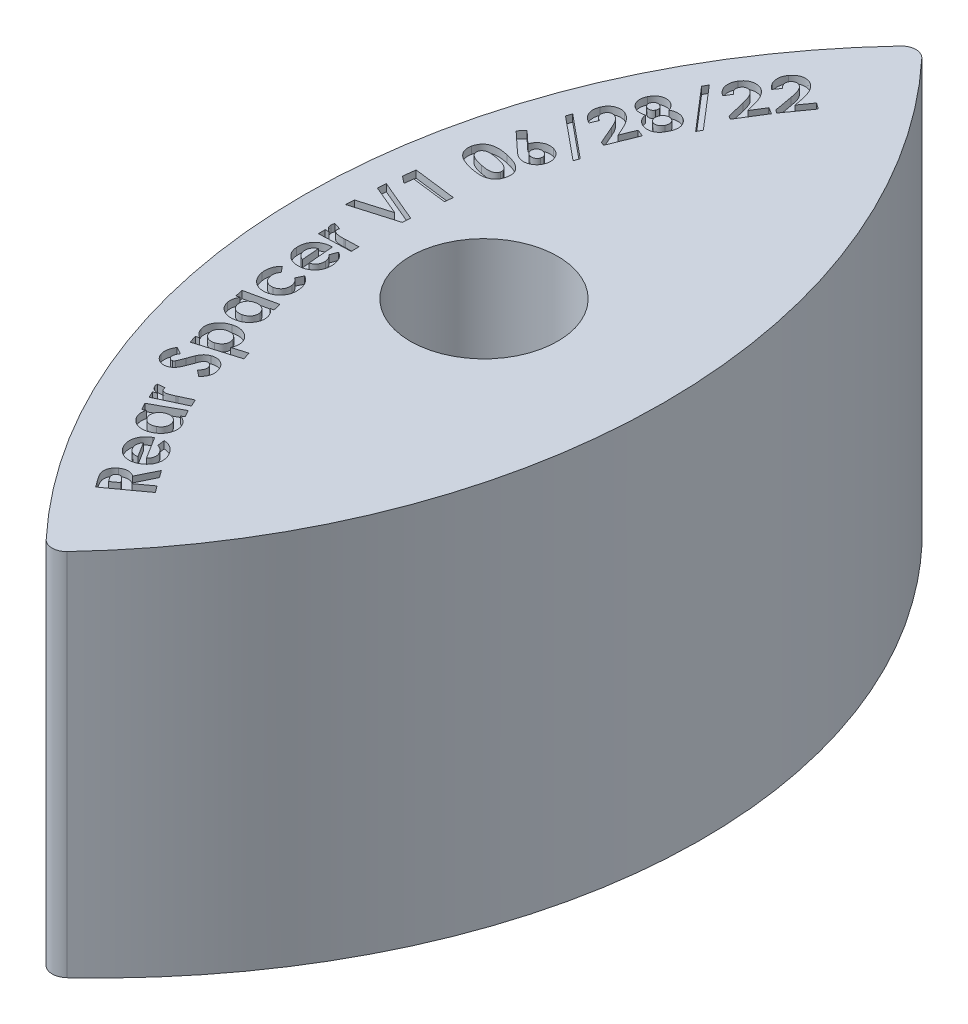
SolidWorks part; units mm, degrees
ref_plane "Front Plane" through (0, 0, 0) normal (0, 0, 1) x (1, 0, 0)
ref_plane "Top Plane" through (0, 0, 0) normal (0, 1, 0) x (1, 0, 0)
ref_plane "Right Plane" through (0, 0, 0) normal (1, 0, 0) x (0, 0, -1)
sketch "Sketch2" plane through (0, 0, 0) normal (1, 0, 0) x (0, 0, -1)
  line L0 (-15.7391, 19.787) -> (12.7788, 17.9806) construction
  line L1 (-38.1, 2.3866) -> (-38.1, 34.925)
  line L2 (-38.1, 34.925) -> (38.1, 34.925)
  line L3 (38.1, 34.925) -> (38.1, -2.4245)
  line L4 (-38.1, 0) -> (38.1, 0) construction
  line L5 (-302.918, -43.2315) -> (-283.9965, -45.4399) construction
  line L6 (-9.9515, 0.403) -> (9.0957, 0.7277) construction
  line L7 (5.0188, 11.0286) -> (23.9594, 8.9897) construction
  spline S0 degree 2 poles (-38.1, 2.3866) (0.0024, 0.0188) (38.1, -2.4245) knots 0 0 0 1 1 1
  point P4 (0, -3.7491)
  point P10 (-38.1, 2.45)
  point P11 (0, 0)
  point P15 (38.1, -2.4245)
  point P16 (0, 0)
  point P17 (0, 0)
  point P22 (-38.1, 2.3866)
  dimension "D1" = 28.575
  dimension "D2" = 34.925
  dimension "D3" = 19.05
  dimension "D4" = 76.2
  dimension "D5" = 19.05
  dimension "D6" = 19.05
extrude "Boss-Extrude1" add sketch "Sketch2" against normal mid plane 31.75
sketch "Sketch3" plane through (0, 34.925, 0) normal (0, 1, 0) x (1, 0, 0)
  line L0 (-15.875, 38.1) -> (-15.875, -38.1) construction
  line L1 (0, 0) -> (0, 38.1) construction
  line L2 (-15.875, 38.1) -> (15.875, 38.1) construction
  line L3 (15.875, 38.1) -> (15.875, -38.1) construction
  line L4 (-15.875, -38.1) -> (15.875, -38.1) construction
  line L9 (15.875, -38.1) -> (15.875, 38.1)
  line L10 (15.875, 38.1) -> (-15.875, 38.1)
  line L11 (-15.875, 38.1) -> (-15.875, -38.1)
  line L12 (-15.875, -38.1) -> (15.875, -38.1)
  line L13 (15.875, -38.1) -> (15.875, 38.1)
  line L14 (15.875, 38.1) -> (-15.875, 38.1)
  line L15 (-15.875, 38.1) -> (-15.875, -38.1)
  line L16 (-15.875, -38.1) -> (15.875, -38.1)
  arc A0 (-0.9249, 37.7004) -> (-0.9249, -37.7004) centre (39.1353, 0) ccw
  arc A1 (0.9249, 37.7004) -> (0.9249, -37.7004) centre (-39.1353, 0) cw
  arc A2 (0.9249, 37.7004) -> (-0.9249, 37.7004) centre (0, 36.83) ccw
  arc A3 (0.9249, -37.7004) -> (-0.9249, -37.7004) centre (0, -36.83) cw
  circle A4 centre (0, 0) radius 6.5
  dimension "D1" = 1.27
  dimension "D3" = 13
  dimension "D2" = 0
extrude "Cut-Extrude1" cut sketch "Sketch3" against normal through all
sketch "Sketch5" plane through (0, 34.925, 0) normal (0, 1, 0) x (1, 0, 0)
  arc A2 (3.6994, 33.3485) -> (3.6994, -33.3485) centre (39.1353, 0) ccw
  arc A3 (3.6138, 33.2573) -> (3.6994, -33.3485) centre (39.1353, 0) ccw
  dimension "D1" = 6.35
sketch "Sketch6" plane through (0, 34.925, 0) normal (0, 1, 0) x (1, 0, 0)
  text T0 "<b>Rear Spacer V1 06/28/22</b>" font "Century Gothic" height 3.81
extrude "Cut-Extrude2" cut sketch "Sketch6" against normal blind 0.635
